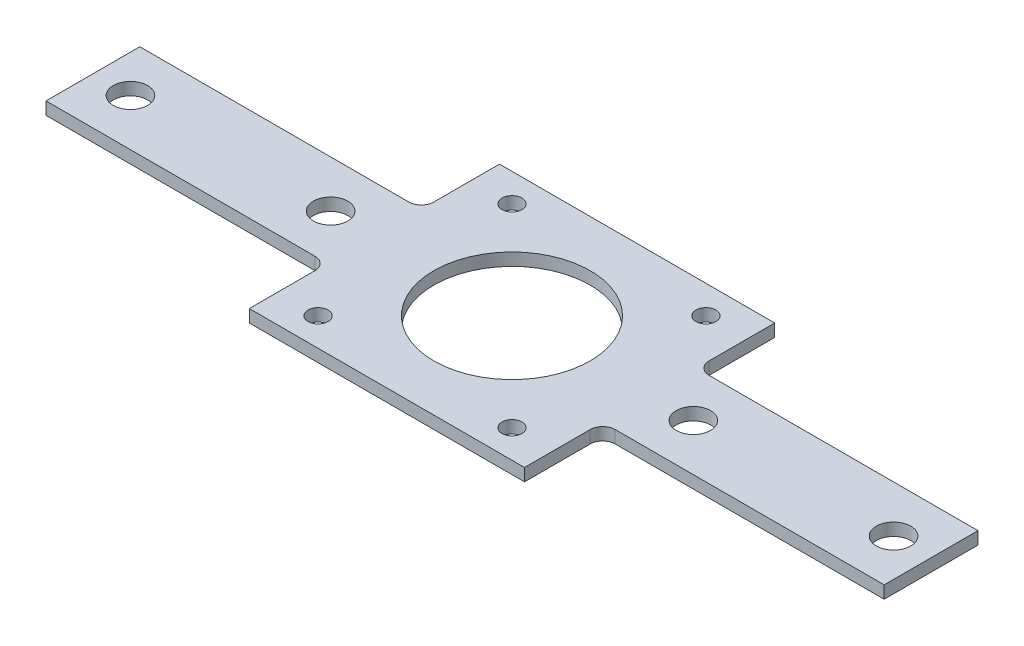
SolidWorks part; units mm, degrees
ref_plane "Plan de face" through (0, 0, 0) normal (0, 0, 1) x (1, 0, 0)
ref_plane "Plan de dessus" through (0, 0, 0) normal (0, 1, 0) x (1, 0, 0)
ref_plane "Plan de droite" through (0, 0, 0) normal (1, 0, 0) x (0, 0, -1)
sketch "Esquisse1" plane through (0, 0, 0) normal (0, 1, 0) x (1, 0, 0)
  line L0 (-23.5, 23.5) -> (23.5, -23.5) construction
  line L1 (-70, 20) -> (70, 20)
  line L2 (-70, 20) -> (-70, -20)
  line L3 (-70, -20) -> (70, -20)
  line L4 (70, 20) -> (70, -20)
  line L5 (-70, 20) -> (70, -20) construction
  line L6 (-70, -20) -> (70, 20) construction
  line L7 (-23.5, 23.5) -> (23.5, 23.5) construction
  line L8 (-23.5, 23.5) -> (-23.5, -23.5) construction
  line L9 (-23.5, -23.5) -> (23.5, -23.5) construction
  line L10 (23.5, 23.5) -> (23.5, -23.5) construction
  line L11 (-23.5, 23.5) -> (23.5, -23.5) construction
  line L12 (-23.5, -23.5) -> (23.5, 23.5) construction
  line L13 (23.5, 23.5) -> (-23.5, -23.5) construction
  line L14 (23.5, -23.5) -> (-23.5, 23.5) construction
  line L34 (-61, 0) -> (61, 0) construction
  line L35 (-15.5, 15.5) -> (15.5, 15.5) construction
  line L36 (-15.5, 15.5) -> (-15.5, -15.5) construction
  line L37 (-15.5, -15.5) -> (15.5, -15.5) construction
  line L38 (15.5, 15.5) -> (15.5, -15.5) construction
  line L39 (-15.5, 15.5) -> (15.5, -15.5) construction
  line L40 (-15.5, -15.5) -> (15.5, 15.5) construction
  circle A0 centre (23.5, 23.5) radius 2.6 construction
  circle A1 centre (23.5, -23.5) radius 2.6 construction
  circle A2 centre (-23.5, -23.5) radius 2.6 construction
  circle A3 centre (-23.5, 23.5) radius 2.6 construction
  circle A4 centre (-61, 0) radius 2.75
  circle A8 centre (0, 0) radius 19.5 construction
  circle A9 centre (-29, 0) radius 2.75
  circle A10 centre (29, 0) radius 2.75
  circle A11 centre (61, 0) radius 2.75
  circle A12 centre (-15.5, 15.5) radius 1.6
  circle A13 centre (15.5, 15.5) radius 1.6
  circle A14 centre (15.5, -15.5) radius 1.6
  circle A15 centre (-15.5, -15.5) radius 1.6
  circle A16 centre (0, 0) radius 12.5
  point P0 (0, 0)
  point P6 (0, 0)
  point P12 (0, 0)
  point P14 (0, 0)
  point P15 (0, 0)
  point P19 (0, 0)
  point P27 (0, 0)
  point P28 (0, 0)
  point P29 (0, 0)
  point P43 (0, 23.5)
  point P53 (0, 0)
  dimension "D5" = 5.2
  dimension "D8" = 5.5
  dimension "D14" = 39
  dimension "D10" = 5.5
  dimension "D11" = 5.5
  dimension "D12" = 5.5
  dimension "D18" = 3.2
  dimension "D20" = 25
  dimension "D1" = 140
  dimension "D2" = 40
  dimension "D3" = 47
  dimension "D4" = 47
  dimension "D9" = 122
  dimension "D15" = 32
  dimension "D16" = 32
  dimension "D17" = 31
  dimension "D7" = 4
  dimension "D19" = 4
extrude "Boss.-Extru.1" add sketch "Esquisse1" along normal blind 2
sketch "Esquisse2" plane through (0, 0, 0) normal (0, -1, 0) x (1, 0, 0)
  line L0 (22, -20) -> (22, -7.5)
  line L2 (70, -20) -> (-70, -20) construction
  line L4 (22, -7.5) -> (67, -7.5)
  line L5 (67, -7.5) -> (67, 7.5)
  line L6 (67, 7.5) -> (22, 7.5)
  line L8 (22, 7.5) -> (22, 20)
  line L9 (-70, 20) -> (70, 20) construction
  line L10 (22, 20) -> (70, 20)
  line L11 (70, 20) -> (70, -20)
  line L12 (70, -20) -> (22, -20)
  line L13 (0, -20) -> (0, 20) construction
  line L14 (-70, 20) -> (-70, -20)
  line L15 (-22, 20) -> (-70, 20)
  line L16 (-22, 7.5) -> (-22, 20)
  line L17 (-67, 7.5) -> (-22, 7.5)
  line L18 (-67, -7.5) -> (-67, 7.5)
  line L19 (-22, -7.5) -> (-67, -7.5)
  line L20 (-22, -20) -> (-22, -7.5)
  line L21 (-70, -20) -> (-22, -20)
  point P12 (67, 0)
  point P13 (70, 0)
  dimension "D1" = 15
  dimension "D2" = 48
  dimension "D3" = 3
extrude "Enlèv. mat.-Extru.1" cut sketch "Esquisse2" against normal up to next
fillet "Congé1" radius 2 4 edges at (-22, 1, 7.5) (-22, 1, -7.5) (22, 1, 7.5) (22, 1, -7.5)
equation "\"D10@Esquisse1\"=\"D8@Esquisse1\""
equation "\"D11@Esquisse1\"=\"D8@Esquisse1\""
equation "\"D12@Esquisse1\"=\"D8@Esquisse1\""
equation "\"D16@Esquisse1\"=\"D15@Esquisse1\""
